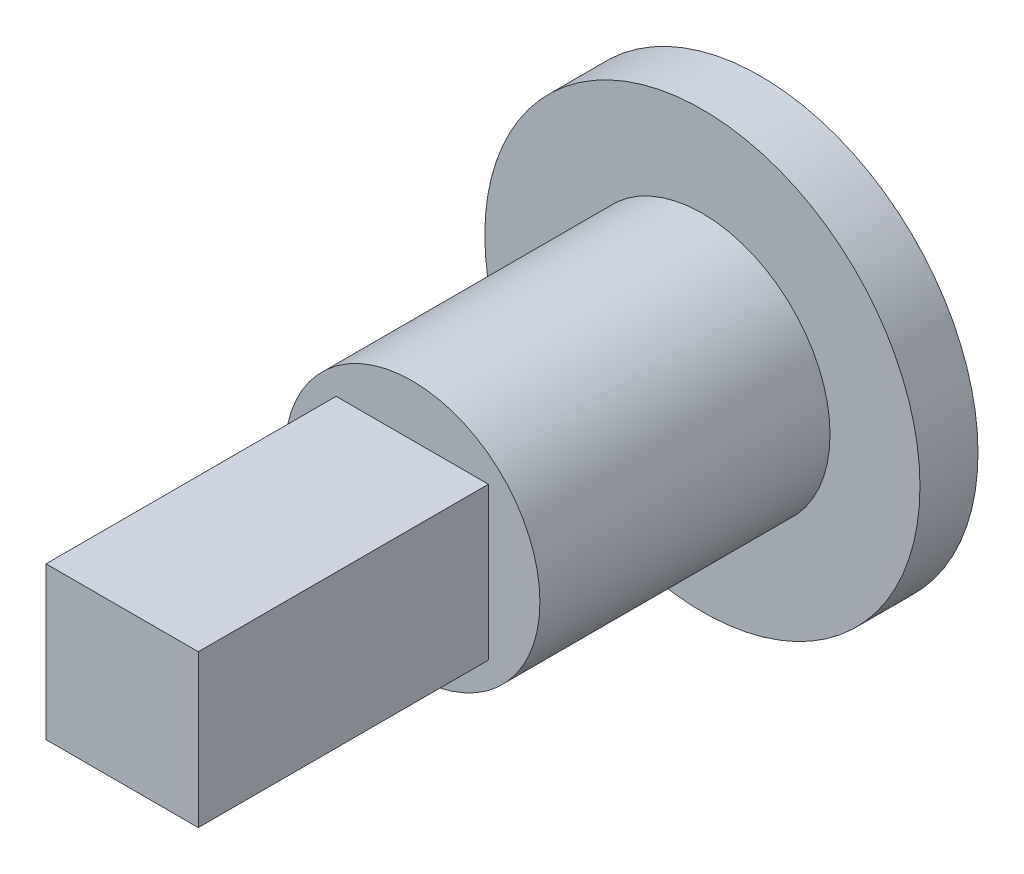
SolidWorks part; units mm, degrees
ref_plane "Front Plane" through (0, 0, 0) normal (0, 0, 1) x (1, 0, 0)
ref_plane "Top Plane" through (0, 0, 0) normal (0, 1, 0) x (1, 0, 0)
ref_plane "Right Plane" through (0, 0, 0) normal (1, 0, 0) x (0, 0, -1)
sketch "Sketch1" plane through (0, 0, 0) normal (0, 0, 1) x (1, 0, 0)
  circle A0 centre (0, 0) radius 4.4
  dimension "D1" = 8.8
extrude "Boss-Extrude1" add sketch "Sketch1" along normal blind 10
sketch "Sketch2" plane through (0, 0, 10) normal (0, 0, 1) x (1, 0, 0)
  line L1 (-2.625, 2.625) -> (2.625, 2.625)
  line L2 (-2.625, 2.625) -> (-2.625, -2.625)
  line L3 (-2.625, -2.625) -> (2.625, -2.625)
  line L4 (2.625, 2.625) -> (2.625, -2.625)
  dimension "D1" = 5.25
  dimension "D2" = 5.25
  dimension "D3" = 2.625
  dimension "D4" = 2.625
extrude "Boss-Extrude2" add sketch "Sketch2" along normal blind 10
sketch "Sketch3" plane through (0, 0, 0) normal (0, 0, -1) x (-1, 0, 0)
  circle A0 centre (0, 0) radius 7.5
  dimension "D1" = 15
extrude "Boss-Extrude3" add sketch "Sketch3" along normal blind 2
equation "\"D3@Sketch2\"=5.25/2"
equation "\"D4@Sketch2\"=5.25/2"
